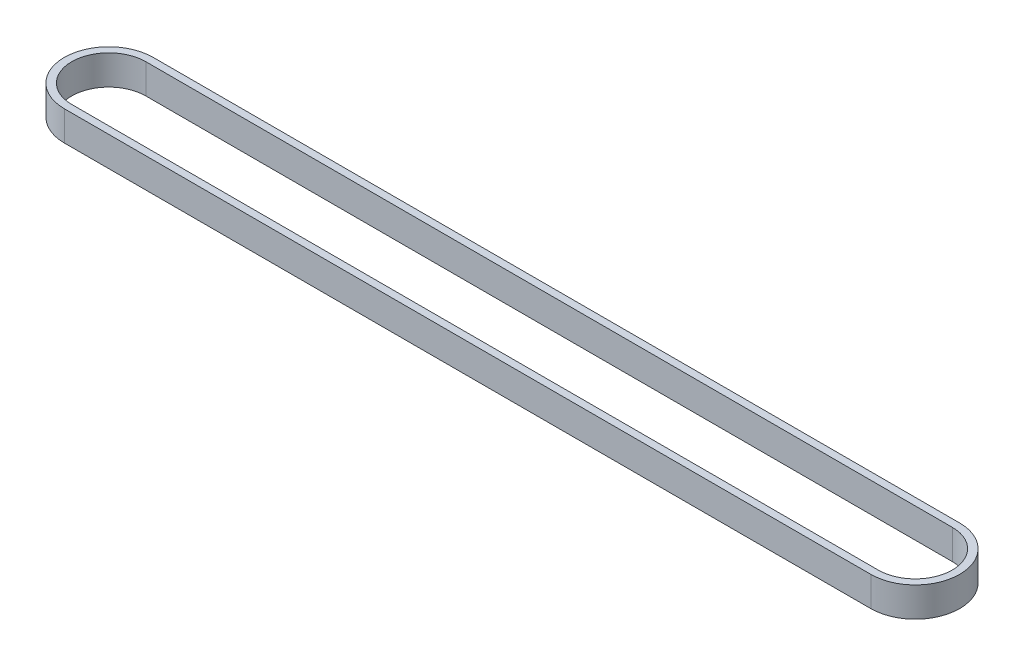
SolidWorks part; units mm, degrees
ref_plane "Front Plane" through (0, 0, 0) normal (0, 0, 1) x (1, 0, 0)
ref_plane "Top Plane" through (0, 0, 0) normal (0, 1, 0) x (1, 0, 0)
ref_plane "Right Plane" through (0, 0, 0) normal (1, 0, 0) x (0, 0, -1)
sketch "Sketch1" plane through (0, 0, 0) normal (0, 1, 0) x (1, 0, 0)
  line L0 (0, 0) -> (217.26, 0) construction
  line L1 (0, 11.975) -> (217.26, 11.975)
  line L2 (0, -11.975) -> (217.26, -11.975)
  line L3 (0, -11.975) -> (0, 11.975) construction
  line L4 (217.26, -11.975) -> (217.26, 11.975) construction
  arc A0 (217.26, -11.975) -> (217.26, 11.975) centre (217.26, 0) ccw
  arc A2 (0, 11.975) -> (0, -11.975) centre (0, 0) ccw
  point P7 (7.1723, 2.1928)
  point P8 (126, 0)
  point P9 (133.1723, 2.1928)
  point P14 (9.5, 0)
  point P16 (135.5, 0)
  dimension "D1" = 11.975
  dimension "D5" = 217.26
extrude "Boss-Extrude2" add sketch "Sketch1" along normal blind 8
sketch "Sketch2" plane through (0, 8, 0) normal (0, 1, 0) x (1, 0, 0)
  line L0 (0, 11.975) -> (217.26, 11.975) construction
  line L1 (0, -11.975) -> (217.26, -11.975) construction
  line L2 (0, 9.975) -> (217.26, 9.975)
  line L3 (0, -9.975) -> (217.26, -9.975)
  arc A1 (217.26, -11.975) -> (217.26, 11.975) centre (217.26, 0) ccw construction
  arc A2 (0, 11.975) -> (0, -11.975) centre (0, 0) ccw construction
  arc A3 (217.26, -9.975) -> (217.26, 9.975) centre (217.26, 0) ccw
  arc A4 (0, 9.975) -> (0, -9.975) centre (0, 0) ccw
  dimension "D1" = 2
extrude "Cut-Extrude1" cut sketch "Sketch2" against normal through all
